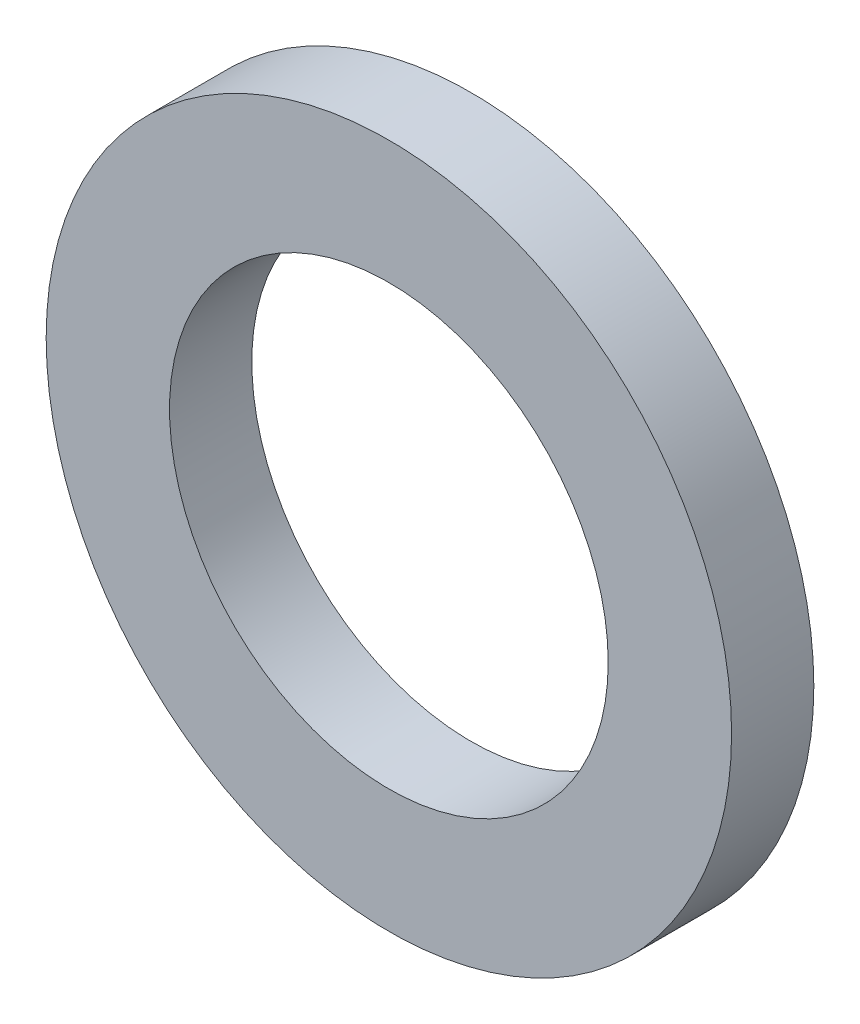
SolidWorks part; units mm, degrees
material "Stainless Steel (ferritic)"
ref_plane "Front Plane" through (0, 0, 0) normal (0, 0, 1) x (1, 0, 0)
ref_plane "Top Plane" through (0, 0, 0) normal (0, 1, 0) x (1, 0, 0)
ref_plane "Right Plane" through (0, 0, 0) normal (1, 0, 0) x (0, 0, -1)
sketch "Sketch1" plane through (0, 0, 0) normal (0, 0, 1) x (1, 0, 0)
  circle A0 centre (0, 0) radius 4
  circle A1 centre (0, 0) radius 6.25
  dimension "D1" = 8
  dimension "D2" = 12.5
extrude "Boss-Extrude1" add sketch "Sketch1" along normal blind 1.5
